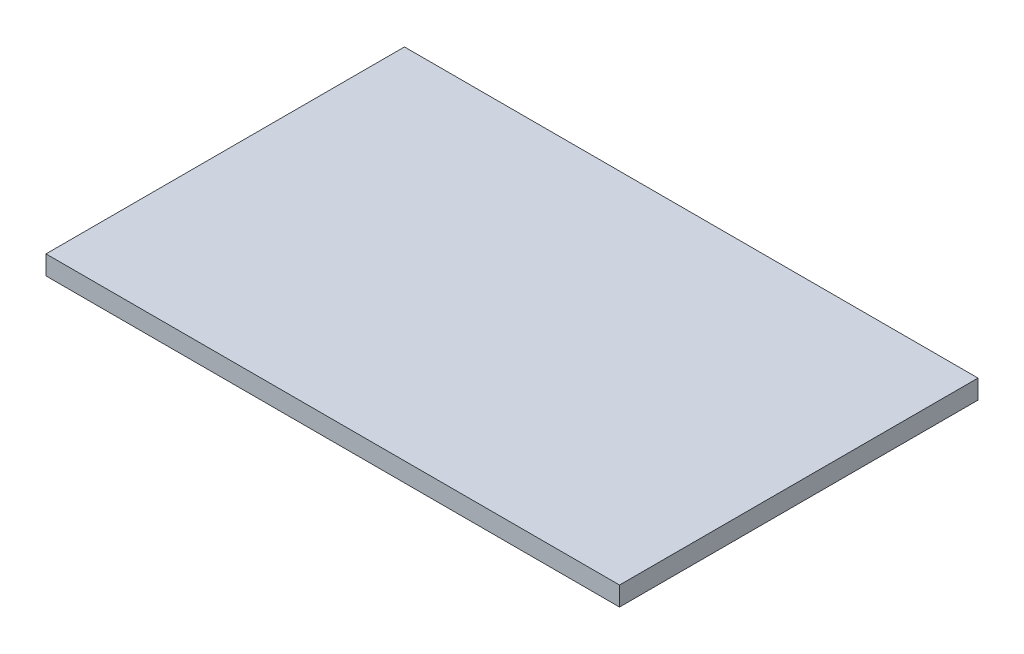
SolidWorks part; units mm, degrees
ref_plane "Front Plane" through (0, 0, 0) normal (0, 0, 1) x (1, 0, 0)
ref_plane "Top Plane" through (0, 0, 0) normal (0, 1, 0) x (1, 0, 0)
ref_plane "Right Plane" through (0, 0, 0) normal (1, 0, 0) x (0, 0, -1)
sketch "Sketch1" plane through (0, 0, 0) normal (0, 1, 0) x (1, 0, 0)
  line L1 (0, 0) -> (48, 0)
  line L2 (0, 0) -> (0, 30)
  line L3 (0, 30) -> (48, 30)
  line L4 (48, 0) -> (48, 30)
  dimension "D1" = 30
  dimension "D2" = 48
extrude "Boss-Extrude1" add sketch "Sketch1" along normal blind 1.6
